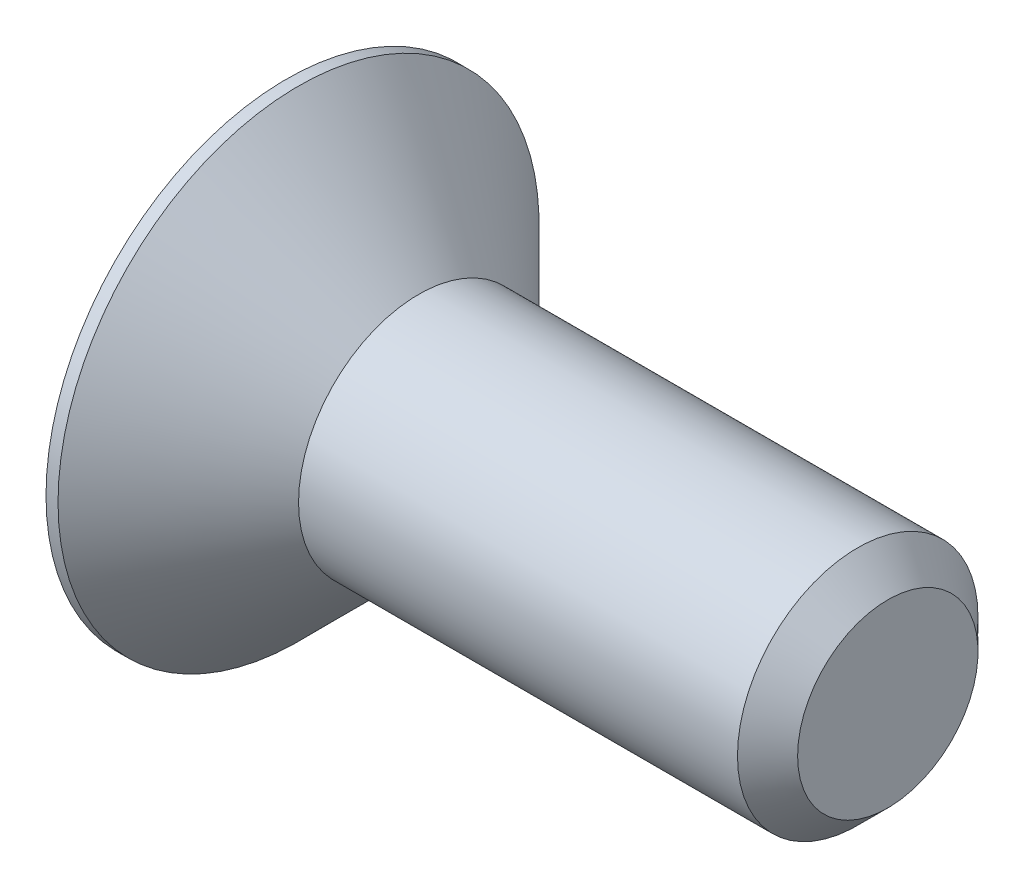
SolidWorks part; units mm, degrees
ref_plane "Front Plane" through (0, 0, 0) normal (0, 0, 1) x (1, 0, 0)
ref_plane "Top Plane" through (0, 0, 0) normal (0, 1, 0) x (1, 0, 0)
ref_plane "Right Plane" through (0, 0, 0) normal (1, 0, 0) x (0, 0, -1)
sketch "Sketch2" plane through (0, 0, 0) normal (0, 0, 1) x (1, 0, 0)
  line L0 (0, 0) -> (0, 2)
  line L1 (0, 2) -> (0.1, 2)
  line L2 (0.1, 2) -> (1.1, 1)
  line L3 (1.1, 1) -> (4.75, 1)
  line L4 (4.75, 1) -> (5, 0.75)
  line L5 (5, 0.75) -> (5, 0)
  line L6 (5, 0) -> (0, 0)
  line L7 (-2.2818, 0) -> (8.0811, 0) construction
  dimension "D1" = 4
  dimension "D2" = 0.1
  dimension "D3" = 45
  dimension "D4" = 5
  dimension "D5" = 0.25
  dimension "D6" = 2
revolve "Revolve1" add sketch "Sketch2" angle 360 about L7
sketch "Sketch3" plane through (0, 0, 0) normal (-1, 0, 0) x (0, 0, 1)
  line L1 (0.433, -0.75) -> (0.866, 0)
  line L2 (0.866, 0) -> (0.433, 0.75)
  line L3 (0.433, 0.75) -> (-0.433, 0.75)
  line L4 (-0.433, 0.75) -> (-0.866, 0)
  line L5 (-0.866, 0) -> (-0.433, -0.75)
  line L6 (-0.433, -0.75) -> (0.433, -0.75)
  circle A0 centre (0, 0) radius 0.75 construction
  dimension "D1" = 1.5
extrude "Cut-Extrude1" cut sketch "Sketch3" against normal blind 0.8
